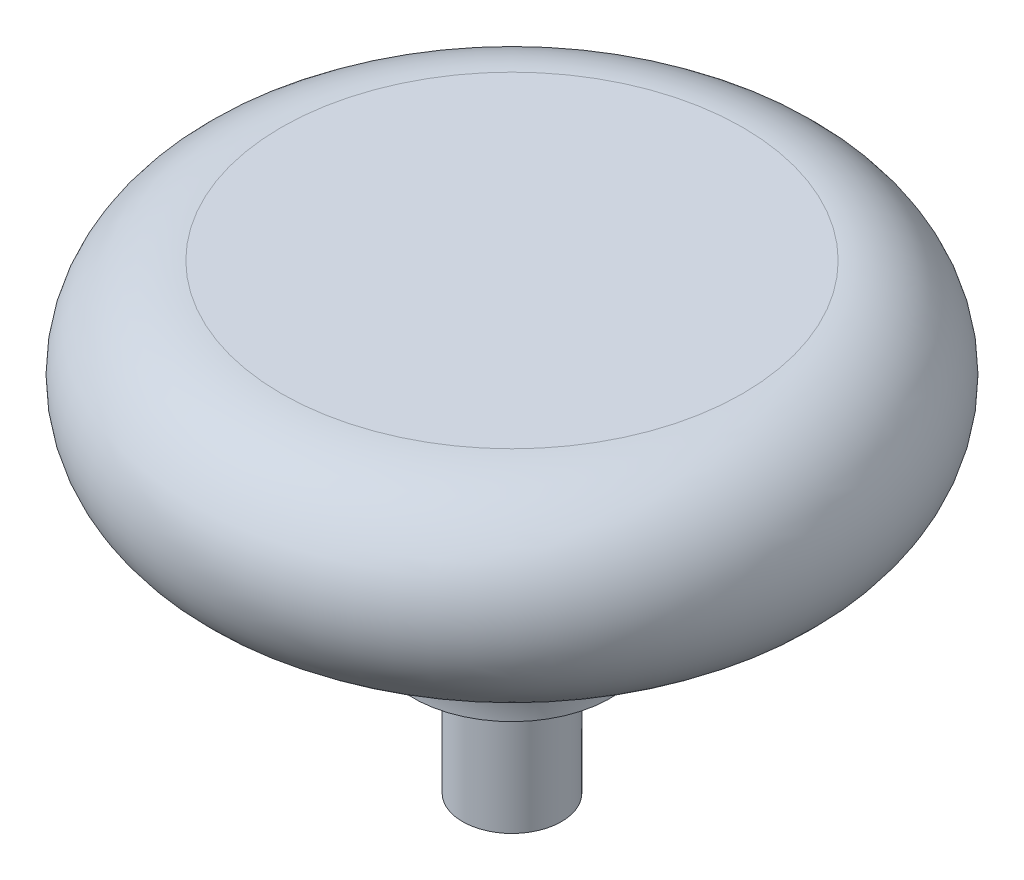
SolidWorks part; units mm, degrees
ref_plane "Front" through (0, 0, 0) normal (0, 0, 1) x (1, 0, 0)
ref_plane "Top" through (0, 0, 0) normal (0, 1, 0) x (-1, 0, 0)
ref_plane "Right" through (0, 0, 0) normal (1, 0, 0) x (0, 0, -1)
sketch "Sketch1" plane through (0, 0, 0) normal (0, 0, 1) x (1, 0, 0)
  line L0 (0, 0) -> (0, 36.2882) construction
  line L1 (0, 0) -> (0, 22.225)
  line L2 (0, 22.225) -> (11.1125, 22.225)
  line L4 (4.7625, 6.35) -> (2.3813, 6.35)
  line L5 (2.3813, 6.35) -> (2.3812, 0)
  line L6 (2.3812, 0) -> (0, 0)
  arc A0 (11.1125, 22.225) -> (11.1125, 12.7) centre (11.1125, 17.4625) cw
  arc A1 (11.1125, 12.7) -> (4.7625, 6.35) centre (11.1125, 6.35) ccw
  dimension "D5" = 6.35
  dimension "D6" = 4.7625
  dimension "D1" = 2.3813
  dimension "D2" = 4.7625
  dimension "D3" = 6.35
  dimension "D4" = 15.875
revolve "Base-Revolve" add sketch "Sketch1" angle 360 about L0
